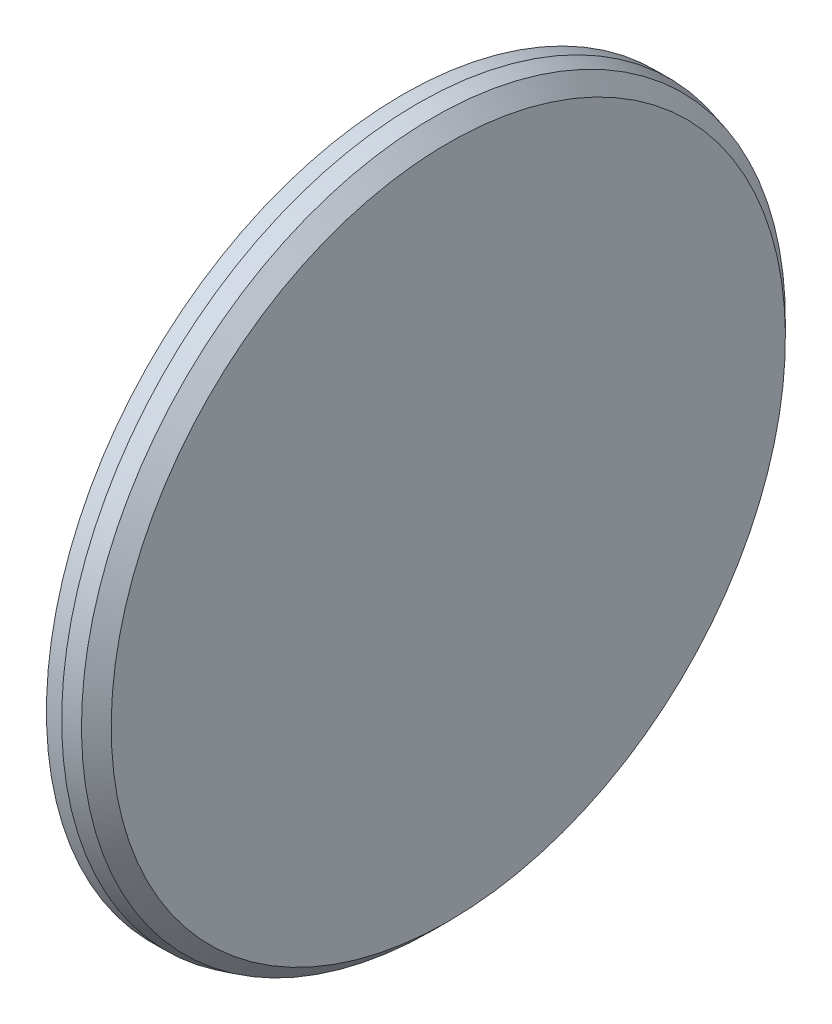
SolidWorks part; units mm, degrees
material "1060 Alloy"
ref_plane "Front Plane" through (0, 0, 0) normal (0, 0, 1) x (1, 0, 0)
ref_plane "Top Plane" through (0, 0, 0) normal (0, 1, 0) x (1, 0, 0)
ref_plane "Right Plane" through (0, 0, 0) normal (1, 0, 0) x (0, 0, -1)
sketch "Sketch1" plane through (0, 0, 0) normal (0, 0, 1) x (1, 0, 0)
  line L0 (-40, 0) -> (40, 0)
  line L1 (-40, 0) -> (-40, 100)
  line L2 (40, 0) -> (40, 100)
  line L4 (-40, 100) -> (10, 100)
  line L5 (10, 100) -> (10, 422.5)
  line L9 (40, 442.5) -> (40, 100)
  line L10 (40, 442.5) -> (20.4904, 462.0096)
  line L11 (20.4904, 462.0096) -> (0, 467.5)
  line L12 (0, 467.5) -> (-20, 467.5)
  line L13 (-20, 467.5) -> (-20, 422.5)
  line L14 (-20, 422.5) -> (10, 422.5)
  point P3 (0, 0)
  dimension "D1" = 80
  dimension "D2" = 100
  dimension "D3" = 30
  dimension "D4" = 20
  dimension "D5" = 45
  dimension "D6" = 467.5
  dimension "D7" = 442.5
  dimension "D8" = 60
  dimension "D9" = 15
  dimension "D10" = 45
revolve "Revolve2" add sketch "Sketch1" angle 360 about L0
sketch "Sketch2" plane through (10, 0, 0) normal (-1, 0, 0) x (0, 0, 1)
  line L0 (0, 467.5) -> (0, -467.5) construction
  line L1 (20, 411.4076) -> (20, 105.8301)
  line L2 (-20, 353.5622) -> (-20, 105.8301)
  line L3 (279.7686, 302.3008) -> (83.3471, 68.2148)
  line L4 (211.9445, 283.7001) -> (52.7054, 93.9263)
  line L5 (408.6304, 51.744) -> (107.6952, -1.319)
  line L6 (344.7179, 81.0916) -> (100.7493, 38.0734)
  line L7 (346.2895, -223.0243) -> (81.6515, -70.2355)
  line L8 (316.1939, -159.4606) -> (101.6515, -35.5945)
  line L9 (121.9158, -393.4371) -> (17.4022, -106.2881)
  line L10 (139.7193, -325.3994) -> (54.9899, -92.6073)
  line L11 (-159.5036, -379.7563) -> (-54.9899, -92.6073)
  line L12 (-102.1316, -339.0802) -> (-17.4022, -106.2881)
  line L13 (-366.2895, -188.3833) -> (-101.6515, -35.5945)
  line L14 (-296.1939, -194.1016) -> (-81.6515, -70.2355)
  line L15 (-401.6845, 91.1363) -> (-100.7493, 38.0734)
  line L16 (-351.6638, 41.6993) -> (-107.6952, -1.319)
  line L17 (-249.1268, 328.0123) -> (-52.7054, 93.9263)
  line L18 (-242.5863, 257.9886) -> (-83.3471, 68.2148)
  circle A0 centre (0, 0) radius 467.5 construction
  arc A1 (-20, 353.5622) -> (-93.2414, 412.0829) centre (-80, 353.5622) ccw
  circle A2 centre (0, 0) radius 422.5 construction
  arc A3 (-20, 105.8301) -> (-27.2727, 96.2091) centre (-30, 105.8301) cw
  circle A4 centre (0, 0) radius 100 construction
  arc A6 (20, 105.8301) -> (27.2727, 96.2091) centre (30, 105.8301) ccw
  arc A7 (20, 411.4076) -> (30.7273, 421.3812) centre (30, 411.4076) cw
  arc A9 (-93.2414, 412.0829) -> (30.7273, 421.3812) centre (0, 0) ccw
  arc A10 (-27.2727, 96.2091) -> (27.2727, 96.2091) centre (0, 0) ccw
  arc A11 (211.9445, 283.7001) -> (193.4547, 375.6082) centre (165.9819, 322.2674) ccw
  arc A12 (279.7686, 302.3008) -> (294.397, 303.0456) centre (287.4291, 295.8729) cw
  arc A13 (52.7054, 93.9263) -> (40.9499, 91.231) centre (45.0449, 100.3542) cw
  arc A14 (83.3471, 68.2148) -> (82.7342, 56.1699) centre (91.0076, 61.7869) ccw
  arc A15 (344.7179, 81.0916) -> (389.6312, 163.3823) centre (334.299, 140.1801) ccw
  arc A16 (408.6304, 51.744) -> (420.3152, 42.9116) centre (410.3669, 41.896) cw
  arc A17 (100.7493, 38.0734) -> (90.0116, 43.5649) centre (99.0128, 47.9214) cw
  arc A18 (107.6952, -1.319) -> (99.4834, -10.1519) centre (109.4317, -11.167) ccw
  arc A19 (316.1939, -159.4606) -> (403.4949, -125.292) centre (346.1939, -107.4991) ccw
  arc A20 (346.2895, -223.0243) -> (349.5632, -237.3012) centre (341.2895, -231.6846) cw
  arc A21 (101.6515, -35.5945) -> (96.9559, -24.4857) centre (106.6515, -26.9343) cw
  arc A22 (81.6515, -70.2355) -> (69.6832, -71.7234) centre (76.6515, -78.8958) ccw
  arc A23 (139.7193, -325.3994) -> (228.5589, -355.3408) centre (196.1008, -304.8782) ccw
  arc A24 (121.9158, -393.4371) -> (115.2467, -406.4781) centre (112.5189, -396.8573) cw
  arc A25 (54.9899, -92.6073) -> (58.5334, -81.0792) centre (64.3868, -89.1871) cw
  arc A26 (17.4022, -106.2881) -> (7.2775, -99.7348) centre (8.0052, -109.7083) ccw
  arc A27 (-102.1316, -339.0802) -> (-53.3224, -419.1217) centre (-45.75, -359.6014) ccw
  arc A28 (-159.5036, -379.7563) -> (-172.995, -385.4594) centre (-168.9005, -376.3361) cw
  arc A29 (-17.4022, -106.2881) -> (-7.2775, -99.7348) centre (-8.0052, -109.7083) cw
  arc A30 (-54.9899, -92.6073) -> (-58.5334, -81.0792) centre (-64.3868, -89.1871) ccw
  arc A31 (-296.1939, -194.1016) -> (-310.2535, -286.7908) centre (-266.1939, -246.0631) ccw
  arc A32 (-366.2895, -188.3833) -> (-380.2904, -184.08) centre (-371.2895, -179.7231) cw
  arc A33 (-81.6515, -70.2355) -> (-69.6832, -71.7234) centre (-76.6515, -78.8958) cw
  arc A34 (-101.6515, -35.5945) -> (-96.9559, -24.4857) centre (-106.6515, -26.9343) ccw
  arc A35 (-351.6638, 41.6993) -> (-422.0136, -20.2674) centre (-362.0827, -17.3892) ccw
  arc A36 (-401.6845, 91.1363) -> (-409.6437, 103.4325) centre (-399.948, 100.9844) cw
  arc A37 (-107.6952, -1.319) -> (-99.4834, -10.1519) centre (-109.4317, -11.167) cw
  arc A38 (-100.7493, 38.0734) -> (-90.0116, 43.5649) centre (-99.0128, 47.9214) ccw
  arc A39 (-242.5863, 257.9886) -> (-336.3088, 255.7394) centre (-288.549, 219.4214) ccw
  arc A40 (-249.1268, 328.0123) -> (-247.3201, 342.5478) centre (-241.4664, 334.4402) cw
  arc A41 (-83.3471, 68.2148) -> (-82.7342, 56.1699) centre (-91.0076, 61.7869) cw
  arc A42 (-52.7054, 93.9263) -> (-40.9499, 91.231) centre (-45.0449, 100.3542) ccw
  point P118 (0, 0)
  dimension "D2" = 20
  dimension "D3" = 60
  dimension "D5" = 9
  dimension "D4" = 10
  dimension "D1" = 20
extrude "Boss-Extrude2" add sketch "Sketch2" along normal offset from surface (20 mm away) 10 up to face at (-20, -422.5, 0)
equation "\"A\"= 60mm"
equation "\"B\"= 935mm"
